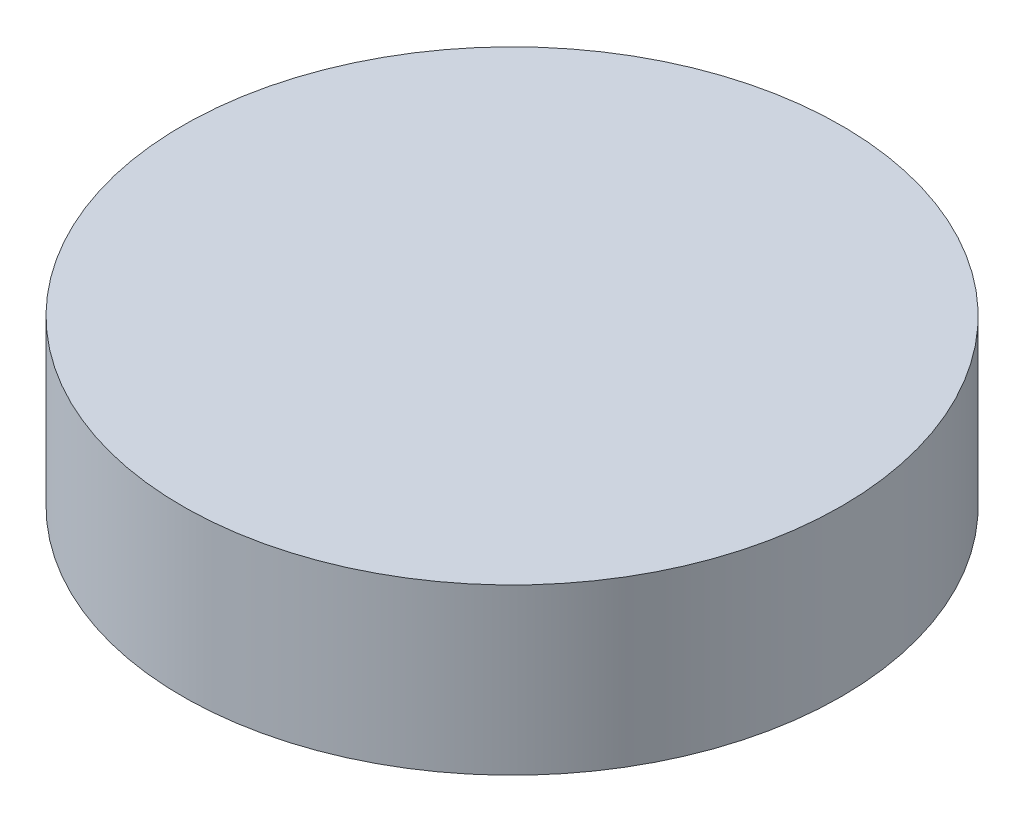
SolidWorks part; units mm, degrees
ref_plane "Front Plane" through (0, 0, 0) normal (0, 0, 1) x (1, 0, 0)
ref_plane "Top Plane" through (0, 0, 0) normal (0, 1, 0) x (1, 0, 0)
ref_plane "Right Plane" through (0, 0, 0) normal (1, 0, 0) x (0, 0, -1)
sketch "Sketch1" plane through (0, 0, 0) normal (0, 0, 1) x (1, 0, 0)
  line L0 (0, -1000) -> (0, -1.8067) construction
  line L1 (-3.8158, 0) -> (-12, 0)
  line L2 (-12, 0) -> (-12, 6)
  line L3 (-12, 6) -> (0, 6)
  line L4 (0, 5.2) -> (0, 6)
  line L5 (0, 5.2) -> (0, 1012.9354) construction
  arc A0 (0, 5.2) -> (-3.8158, 0) centre (0, 1.2) ccw
  point P9 (0, -1.3559)
  point P10 (0, -1.3559)
  point P11 (0, -1.3559)
  point P12 (0, 1.279)
  dimension "D3" = 1.2
  dimension "D1" = 4
  dimension "D2" = 6
revolve "Revolve1" add sketch "Sketch1" angle 360 about L5
